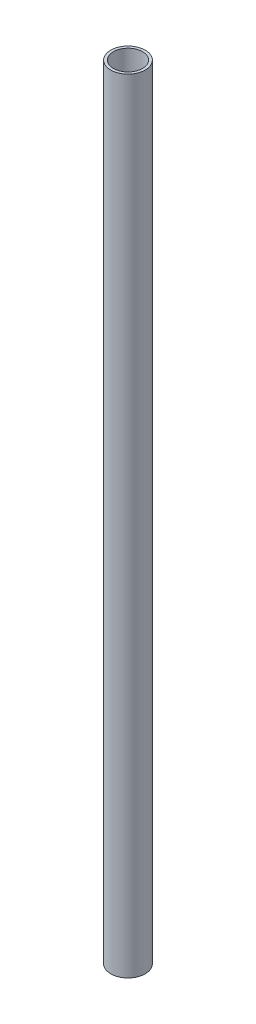
SolidWorks part; units mm, degrees
material "普通碳钢"
ref_plane "前视基准面" through (0, 0, 0) normal (0, 0, 1) x (1, 0, 0)
ref_plane "上视基准面" through (0, 0, 0) normal (0, 1, 0) x (1, 0, 0)
ref_plane "右视基准面" through (0, 0, 0) normal (1, 0, 0) x (0, 0, -1)
sketch "草图1" plane through (0, 0, 0) normal (0, 1, 0) x (1, 0, 0)
  circle A0 centre (0, 0) radius 11
  circle A1 centre (0, 0) radius 13
  dimension "D1" = 22
  dimension "D2" = 26
extrude "凸台-拉伸1" add sketch "草图1" along normal blind 590
sketch "草图2" plane through (0, 0, 0) normal (1, 0, 0) x (0, 0, -1)
  line L0 (0, 0) -> (0, 590) construction
  line L1 (11, 590) -> (-11, 590) construction
  circle A0 centre (0, 22.5) radius 1.5
  circle A1 centre (0, 571.5) radius 1.5
  dimension "D1" = 3
  dimension "D2" = 3
  dimension "D3" = 22.5
  dimension "D4" = 18.5
